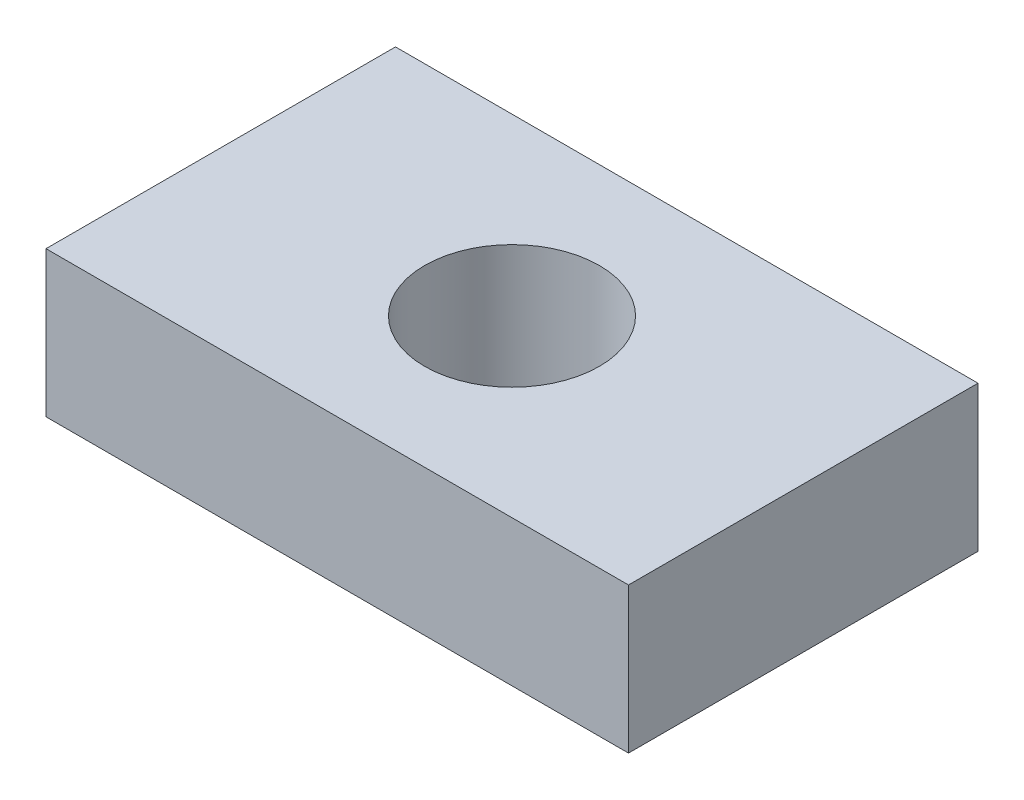
SolidWorks part; units mm, degrees
material "Plain Carbon Steel"
ref_plane "Front Plane" through (0, 0, 0) normal (0, 0, 1) x (1, 0, 0)
ref_plane "Top Plane" through (0, 0, 0) normal (0, 1, 0) x (1, 0, 0)
ref_plane "Right Plane" through (0, 0, 0) normal (1, 0, 0) x (0, 0, -1)
sketch "Sketch1" plane through (0, 0, 0) normal (0, 1, 0) x (1, 0, 0)
  line L1 (-5, -3) -> (5, -3)
  line L2 (-5, -3) -> (-5, 3)
  line L3 (-5, 3) -> (5, 3)
  line L4 (5, -3) -> (5, 3)
  line L5 (0, 3) -> (0, -3) construction
  line L6 (-5, 0) -> (5, 0) construction
  circle A0 centre (0, 0) radius 1.5
  point P0 (0, 0)
  dimension "D3" = 3
  dimension "D1" = 6
  dimension "D2" = 10
extrude "Boss-Extrude1" add sketch "Sketch1" along normal blind 2.5
